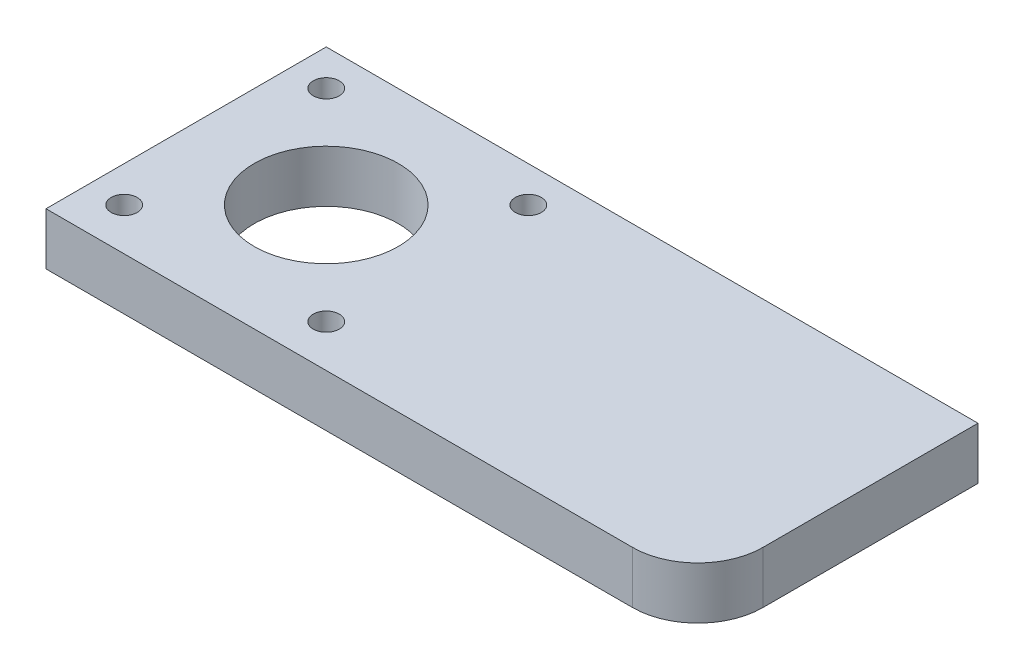
SolidWorks part; units mm, degrees
material "Клен"
ref_plane "Спереди" through (0, 0, 0) normal (0, 0, 1) x (1, 0, 0)
ref_plane "Сверху" through (0, 0, 0) normal (0, 1, 0) x (1, 0, 0)
ref_plane "Справа" through (0, 0, 0) normal (1, 0, 0) x (0, 0, -1)
sketch "Эскиз1" plane through (0, 0, 0) normal (0, 1, 0) x (1, 0, 0)
  line L0 (-29, 25.0857) -> (-29, -26) construction
  line L1 (-50, -21.5) -> (40, -21.5)
  line L2 (-50, -21.5) -> (-50, 21.5)
  line L3 (-50, 21.5) -> (50, 21.5)
  line L4 (50, -11.5) -> (50, 21.5)
  line L5 (-50, -21.5) -> (50, 21.5) construction
  line L6 (-50, 21.5) -> (50, -21.5) construction
  line L7 (-63.7178, 0.5) -> (-6.2323, 0.5) construction
  arc A0 (40, -21.5) -> (50, -11.5) centre (40, -11.5) ccw
  circle A1 centre (-29, 0.5) radius 11.05
  circle A3 centre (-13.5, -15) radius 2
  circle A4 centre (-13.5, 16) radius 2
  circle A5 centre (-44.5, -15) radius 2
  circle A6 centre (-44.5, 16) radius 2
  point P0 (0, 0)
  point P19 (0, 0)
  point P20 (0, 0)
  dimension "D3" = 10
  dimension "D4" = 22.1
  dimension "D5" = 4
  dimension "D1" = 100
  dimension "D2" = 43
  dimension "D6" = 15.5
  dimension "D7" = 15.5
extrude "Бобышка-Вытянуть1" add sketch "Эскиз1" along normal blind 8
equation "\"D7@Эскиз1\"=\"D6@Эскиз1\""
